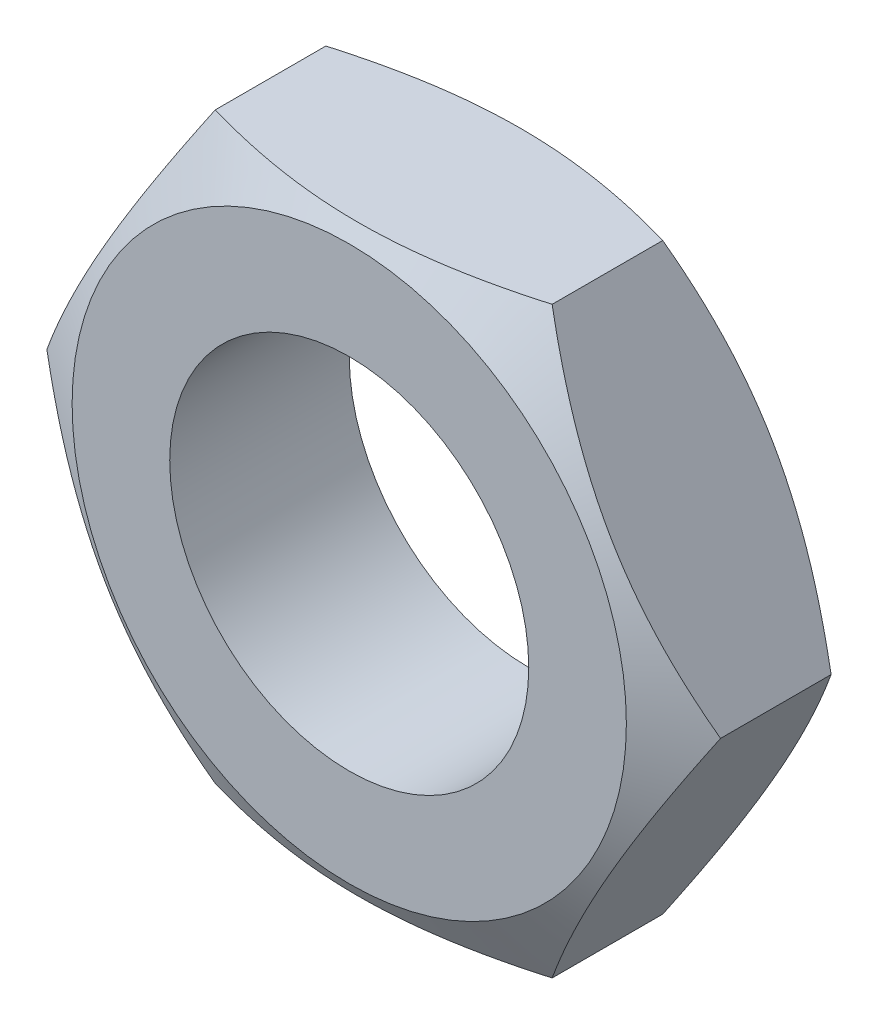
SolidWorks part; units mm, degrees
ref_plane "Plane1" through (0, 0, 0) normal (0, 0, 1) x (1, 0, 0)
ref_plane "Plane2" through (0, 0, 0) normal (0, 1, 0) x (1, 0, 0)
ref_plane "Plane3" through (0, 0, 0) normal (1, 0, 0) x (0, 0, -1)
sketch "BaseNutSke" plane through (0, 0, 0) normal (0, 0, 1) x (1, 0, 0)
  line L6 (3.7528, -6.5) -> (-3.7528, -6.5)
  line L7 (3.7528, 6.5) -> (-3.7528, 6.5)
  line L8 (3.7528, -6.5) -> (7.5056, 0)
  line L9 (7.5056, 0) -> (3.7528, 6.5)
  line L10 (-3.7528, 6.5) -> (-7.5056, 0)
  line L11 (-7.5056, 0) -> (-3.7528, -6.5)
  circle A0 centre (0, 0) radius 3.4 construction
  circle A1 centre (0, 0) radius 7.5056 construction
  circle A2 centre (0, 0) radius 4
  dimension "Tap_drill" = 6.8
  dimension "Diameter" = 8
  dimension "Width_flats" = 13
extrude "BaseNut" add sketch "BaseNutSke" against normal blind 4
cosmetic thread "ThreadCosmetic" [suppressed] parameters "Thread_major"=8
ref_plane "Plane4" through (0, 0, -2) normal (0, 0, -1) x (-1, 0, 0)
sketch "Sketch6" plane through (0, 0, -4) normal (0, 0, -1) x (-1, 0, 0)
  circle A0 centre (0, 0) radius 6.175
  dimension "D1" = 12.35
extrude "Cut-Extrude2" cut sketch "Sketch6" against normal through all draft 60 flip side to cut
mirror "Mirror1" about plane through (0, 0, -2) normal (0, 0, -1) of "Cut-Extrude2"
equation "\"D1@Sketch3\" = \"Width_flats@BaseNutSke\" /2"
equation "' \"Num_threads@ThdSchPat\" = \"Num_threads@ThdSchPat\" - sgn( \"Num_threads@ThdSchPat\" - 1) '---chamfered tips only---"
equation "\"D1@Sketch6\" = 0.95 * \"Width_flats@BaseNutSke\""
